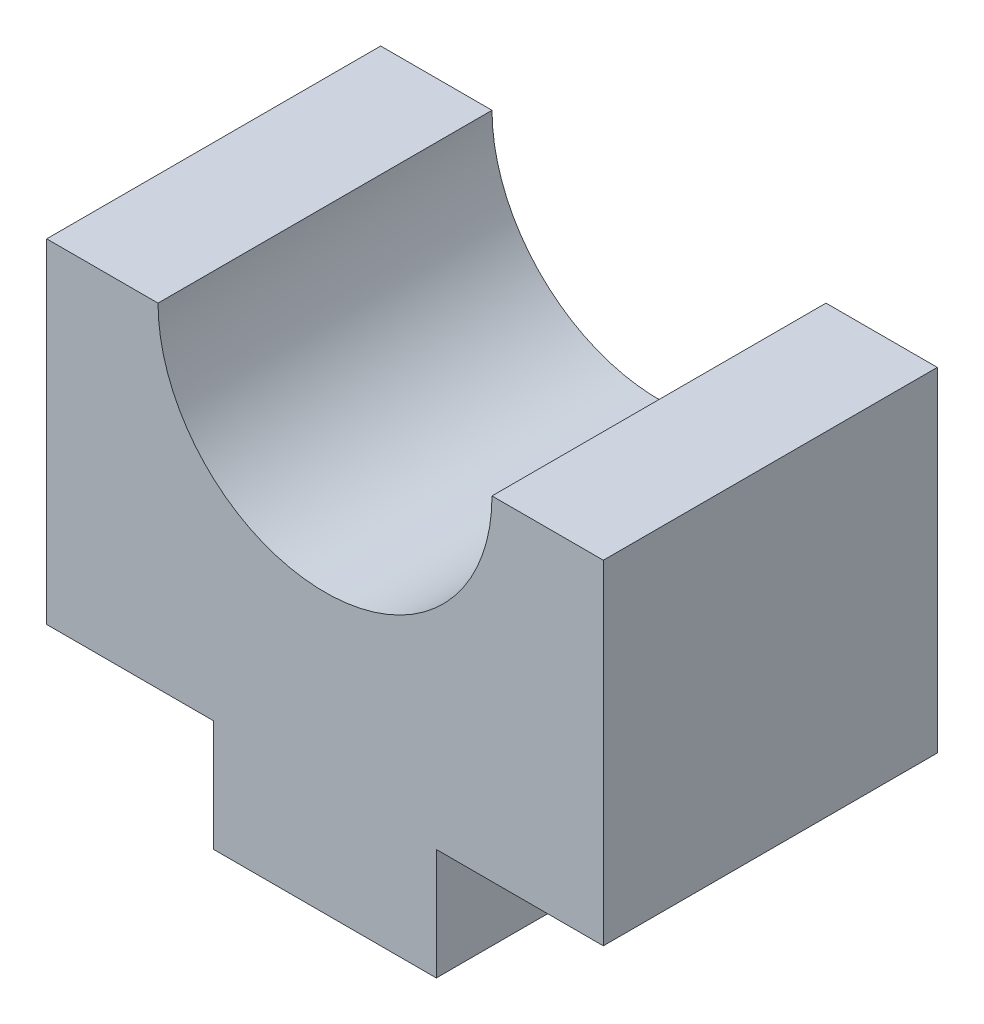
SolidWorks part; units mm, degrees
ref_plane "Alzado" through (0, 0, 0) normal (0, 0, 1) x (1, 0, 0)
ref_plane "Planta" through (0, 0, 0) normal (0, 1, 0) x (1, 0, 0)
ref_plane "Vista lateral" through (0, 0, 0) normal (1, 0, 0) x (0, 0, -1)
sketch "Croquis1" plane through (0, 0, 0) normal (0, 1, 0) x (1, 0, 0)
  line L1 (0, 0) -> (25, 0)
  line L2 (0, 0) -> (0, -15)
  line L3 (0, -15) -> (25, -15)
  line L4 (25, 0) -> (25, -15)
  dimension "D1" = 15
  dimension "D2" = 25
extrude "Saliente-Extruir1" add sketch "Croquis1" along normal blind 20
sketch "Croquis2" plane through (0, 0, 15) normal (0, 0, 1) x (1, 0, 0)
  line L0 (25, 0) -> (17.5, 0)
  line L1 (0, 0) -> (25, 0) construction
  line L2 (17.5, 0) -> (17.5, 5)
  line L3 (17.5, 5) -> (25, 5)
  line L4 (25, 20) -> (25, 0) construction
  line L5 (25, 5) -> (25, 0)
  line L6 (12.5, 20) -> (12.5, 0) construction
  line L7 (0, 20) -> (25, 20) construction
  line L8 (7.5, 5) -> (0, 5)
  line L9 (7.5, 0) -> (7.5, 5)
  line L10 (0, 0) -> (7.5, 0)
  line L11 (0, 5) -> (0, 0)
extrude "Cortar-Extruir1" cut sketch "Croquis2" against normal blind 20
sketch "Croquis3" plane through (0, 0, 15) normal (0, 0, 1) x (1, 0, 0)
  line L0 (25, 15) -> (25, 10)
  line L1 (25, 20) -> (20, 20)
  line L2 (25, 20) -> (25, 15)
  line L7 (25, 10) -> (20, 10)
  line L8 (25, 10) -> (25, 5)
  line L9 (25, 10) -> (20, 10)
  line L10 (20, 10) -> (20, 5)
  line L11 (25, 5) -> (20, 5)
  line L13 (20, 20) -> (15, 20)
  line L17 (20, 10) -> (15, 10)
  line L20 (20, 10) -> (20, 5)
  line L21 (20, 5) -> (15, 5)
  line L22 (15, 10) -> (15, 5)
  line L23 (20, 10) -> (15, 10)
  line L25 (15, 20) -> (10, 20)
  line L29 (15, 10) -> (10, 10)
  line L32 (15, 10) -> (15, 5)
  line L33 (15, 5) -> (10, 5)
  line L34 (10, 10) -> (10, 5)
  line L35 (15, 10) -> (10, 10)
  line L41 (10, 10) -> (5, 10)
  line L44 (10, 10) -> (10, 5)
  line L45 (10, 5) -> (5, 5)
  line L46 (5, 10) -> (5, 5)
  line L47 (10, 10) -> (5, 10)
  line L49 (5, 20) -> (0, 20)
  line L50 (0, 20) -> (0, 15)
  line L51 (5, 15) -> (0, 15)
  line L53 (5, 10) -> (0, 10)
  line L54 (0, 15) -> (0, 10)
  line L55 (5, 15) -> (0, 15)
  line L56 (5, 10) -> (5, 5)
  line L57 (5, 5) -> (0, 5)
  line L58 (0, 10) -> (0, 5)
  line L59 (5, 10) -> (0, 10)
  line L62 (5, 20) -> (5, 15) [skipped]
  line L63 (5, 15) -> (5, 10) [skipped]
  line L64 (5, 27.5) -> (5, 12.5)
  line L65 (12.5, 20) -> (12.5, 5) construction
  line L66 (20, 27.5) -> (20, 12.5)
  line L67 (20, 20) -> (20, 15) [skipped]
  line L68 (20, 15) -> (20, 10) [skipped]
  line L69 (5, 12.5) -> (20, 12.5)
  line L70 (5, 27.5) -> (20, 27.5)
  line L71 (10, 15) -> (10, 10) [skipped]
  line L72 (10, 20) -> (10, 15) [skipped]
  line L73 (15, 15) -> (15, 10) [skipped]
  line L76 (15, 20) -> (15, 15) [skipped]
  line L78 (25, 15) -> (20, 15) [skipped]
  line L79 (10, 20) -> (5, 20) [skipped]
  circle A0 centre (12.5, 20) radius 7.5
  dimension "D5" = 7.5
  dimension "D3" = 3
  dimension "D4" = 5
extrude "Cortar-Extruir2" cut sketch "Croquis3" against normal blind 20 contours L0 L65 A0 | L65 L25 L0 A0
